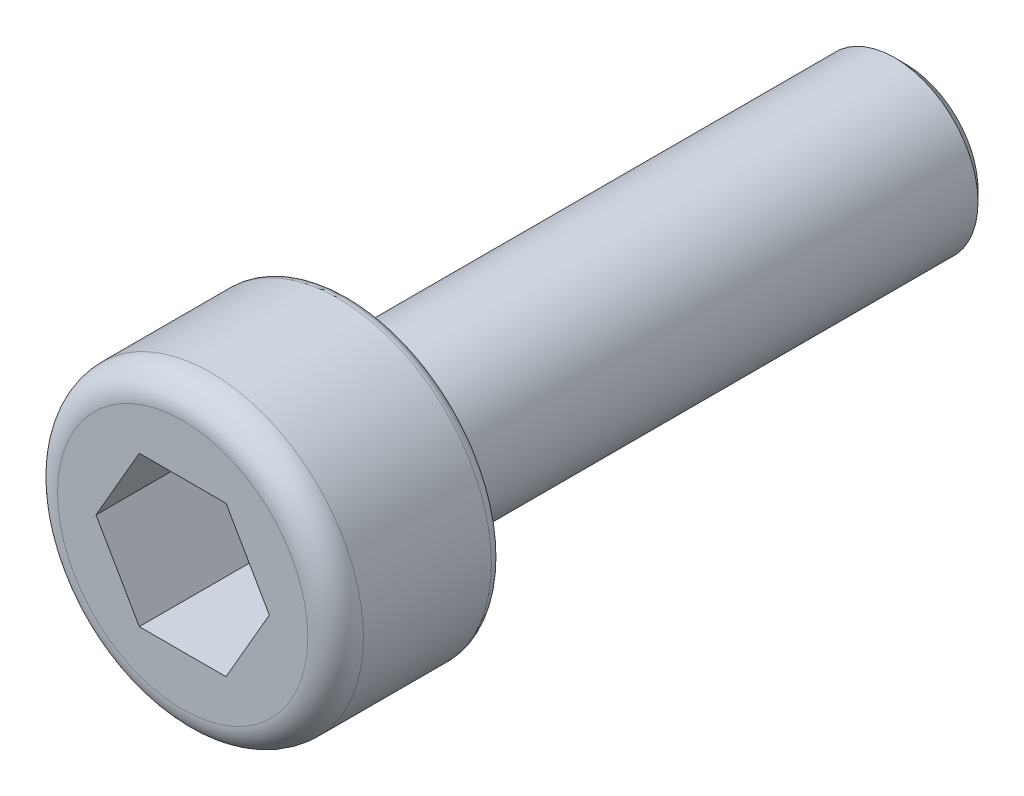
SolidWorks part; units mm, degrees
ref_plane "前视" through (0, 0, 0) normal (0, 0, 1) x (1, 0, 0)
ref_plane "上视" through (0, 0, 0) normal (0, 1, 0) x (1, 0, 0)
ref_plane "右视" through (0, 0, 0) normal (1, 0, 0) x (0, 0, -1)
sketch "草图1" plane through (0, 0, 0) normal (0, 0, 1) x (1, 0, 0)
  circle A0 centre (0, 0) radius 2.75
  dimension "D1" = 5.5
extrude "凸台-拉伸1" add sketch "草图1" along normal blind 3
fillet "圆角1" radius 0.5 1 edges at (2.75, 0, 3)
sketch "草图2" plane through (0, 0, 3) normal (0, 0, 1) x (1, 0, 0)
  line L1 (1.5588, 0) -> (0.7794, 1.35)
  line L2 (0.7794, 1.35) -> (-0.7794, 1.35)
  line L3 (-0.7794, 1.35) -> (-1.5588, 0)
  line L4 (-1.5588, 0) -> (-0.7794, -1.35)
  line L5 (-0.7794, -1.35) -> (0.7794, -1.35)
  line L6 (0.7794, -1.35) -> (1.5588, 0)
  circle A0 centre (0, 0) radius 1.35 construction
  dimension "D1" = 2.7
extrude "切除-拉伸1" cut sketch "草图2" against normal blind 2
sketch "草图3" plane through (0, 0, 0) normal (0, 0, -1) x (-1, 0, 0)
  circle A0 centre (0, 0) radius 1.5
  dimension "D1" = 3
extrude "凸台-拉伸2" add sketch "草图3" along normal blind 10
chamfer "倒角1" distance 0.2 angle 45 1 edges at (-1.5, 0, -10)
fillet "圆角2" radius 0.2 1 edges at (2.75, 0, 0)
